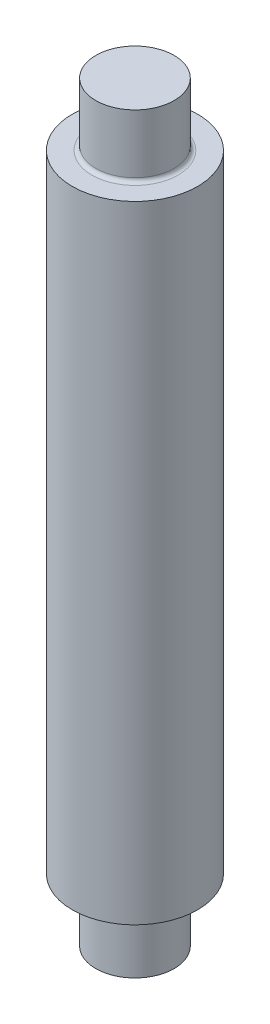
SolidWorks part; units mm, degrees
material "ASTM A36 Steel"
ref_plane "Front Plane" through (0, 0, 0) normal (0, 0, 1) x (1, 0, 0)
ref_plane "Top Plane" through (0, 0, 0) normal (0, 1, 0) x (1, 0, 0)
ref_plane "Right Plane" through (0, 0, 0) normal (1, 0, 0) x (0, 0, -1)
sketch "Sketch1" plane through (0, 0, 0) normal (0, 0, 1) x (1, 0, 0)
  line L0 (0, 76.2) -> (0, -76.2) construction
  line L1 (0, 76.2) -> (-7.9375, 76.2)
  line L2 (-7.9375, 76.2) -> (-7.9375, 64.2938)
  line L3 (-8.7312, 63.5) -> (-12.7, 63.5)
  line L4 (-12.7, 63.5) -> (-12.7, -63.5)
  line L5 (55, 0) -> (-55, 0) construction
  line L6 (-12.7, -63.5) -> (-8.7312, -63.5)
  line L7 (-7.9375, -64.2938) -> (-7.9375, -76.2)
  line L8 (-7.9375, -76.2) -> (0, -76.2)
  line L9 (0, 76.2) -> (0, -76.2)
  arc A0 (-7.9375, 64.2938) -> (-8.7312, 63.5) centre (-8.7312, 64.2938) cw
  arc A1 (-8.7312, -63.5) -> (-7.9375, -64.2938) centre (-8.7312, -64.2938) cw
  point P8 (-12.7, 0)
  dimension "D2" = 0.7937
  dimension "D1" = 15.875
  dimension "D3" = 25.4
  dimension "D4" = 12.7
  dimension "D5" = 152.4
revolve "Revolve1" add sketch "Sketch1" angle 360 mid plane about L0
